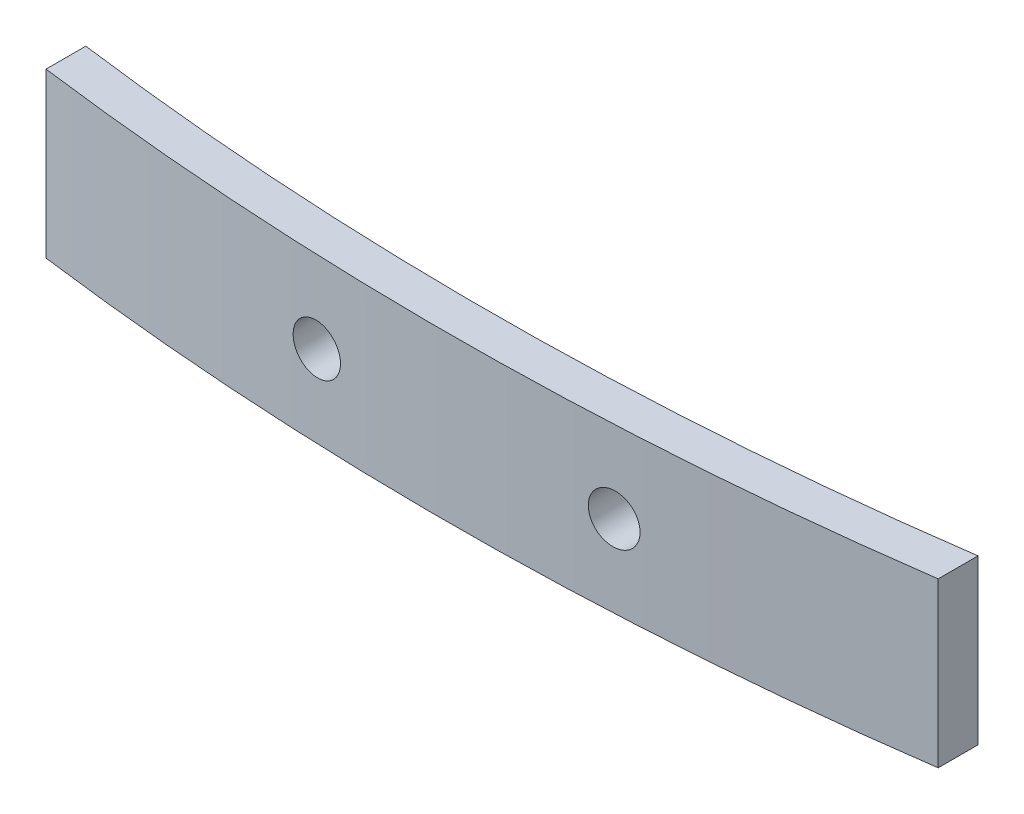
SolidWorks part; units mm, degrees
ref_plane "Front Plane" through (0, 0, 0) normal (0, 0, 1) x (1, 0, 0)
ref_plane "Top Plane" through (0, 0, 0) normal (0, 1, 0) x (1, 0, 0)
ref_plane "Right Plane" through (0, 0, 0) normal (1, 0, 0) x (0, 0, -1)
sketch "Sketch1" plane through (0, 0, 0) normal (0, 1, 0) x (1, 0, 0)
  line L0 (-35, 4.1426) -> (35, 4.5206) construction
  line L4 (22.5, 0.9605) -> (22.5, -1.0596)
  line L9 (-22.5, 11.9983) -> (-22.5, -12.2817) construction
  line L10 (22.5, 11.9983) -> (22.5, -13.4183) construction
  line L12 (-22.5, 0.7227) -> (-22.5, -1.2945)
  arc A4 (-22.5, 0.7227) -> (22.5, 0.9605) centre (-0.865, 164.5106) ccw
  arc A5 (-22.5, -1.2945) -> (22.5, -1.0596) centre (-0.865, 164.5106) ccw
  arc A7 (-35, 2.8648) -> (35, 3.2398) centre (-0.865, 164.5106) ccw construction
  arc A9 (-35.4132, 0.908) -> (35.4342, 1.2875) centre (-0.865, 164.5106) ccw construction
  point P4 (-35, 4.1426)
  point P7 (38.108, 5.4708)
  point P8 (35, 4.5206)
  point P18 (-31.892, 5.0928)
  dimension "D1" = 45
  dimension "D2" = 22.5
  dimension "D3" = 70
  dimension "D4" = 35
  dimension "D7" = 2
extrude "Boss-Extrude1" add sketch "Sketch1" along normal blind 8.3
sketch "Sketch2" plane through (0, 0, 0) normal (0, 0, 1) x (1, 0, 0)
  line L0 (0, 8.3) -> (0, 0) construction
  line L1 (22.5, 8.3) -> (-22.5, 8.3) construction
  circle A0 centre (7.5, 4.15) radius 1.25
  circle A1 centre (-7.5, 4.15) radius 1.25
  point P15 (0, 4.15)
  dimension "D2" = 2.5
  dimension "D3" = 2.5
  dimension "D1" = 15
  dimension "D4" = 7.5
extrude "Cut-Extrude1" cut sketch "Sketch2" against normal through all both and the other way through all
